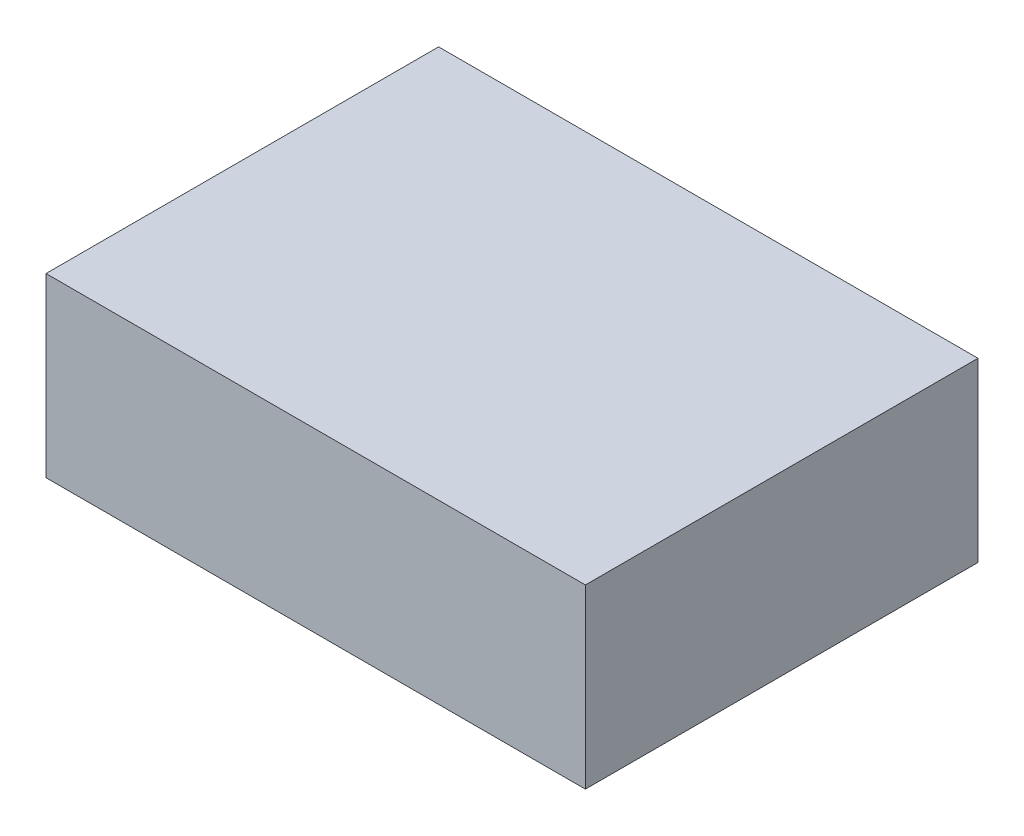
SolidWorks part; units mm, degrees
ref_plane "Front Plane" through (0, 0, 0) normal (0, 0, 1) x (1, 0, 0)
ref_plane "Top Plane" through (0, 0, 0) normal (0, 1, 0) x (1, 0, 0)
ref_plane "Right Plane" through (0, 0, 0) normal (1, 0, 0) x (0, 0, -1)
sketch "Sketch1" plane through (0, 0, 0) normal (0, 1, 0) x (1, 0, 0)
  line L1 (-38.1685, 66.1473) -> (-7.6685, 66.1473)
  line L2 (-38.1685, 66.1473) -> (-38.1685, 43.9473)
  line L3 (-38.1685, 43.9473) -> (-7.6685, 43.9473)
  line L4 (-7.6685, 66.1473) -> (-7.6685, 43.9473)
  line L5 (-38.1685, 66.1473) -> (-7.6685, 43.9473) construction
  line L6 (-38.1685, 43.9473) -> (-7.6685, 66.1473) construction
  point P0 (-22.9185, 55.0473)
  dimension "D1" = 22.2
  dimension "D2" = 30.5
extrude "Boss-Extrude1" add sketch "Sketch1" along normal blind 10
